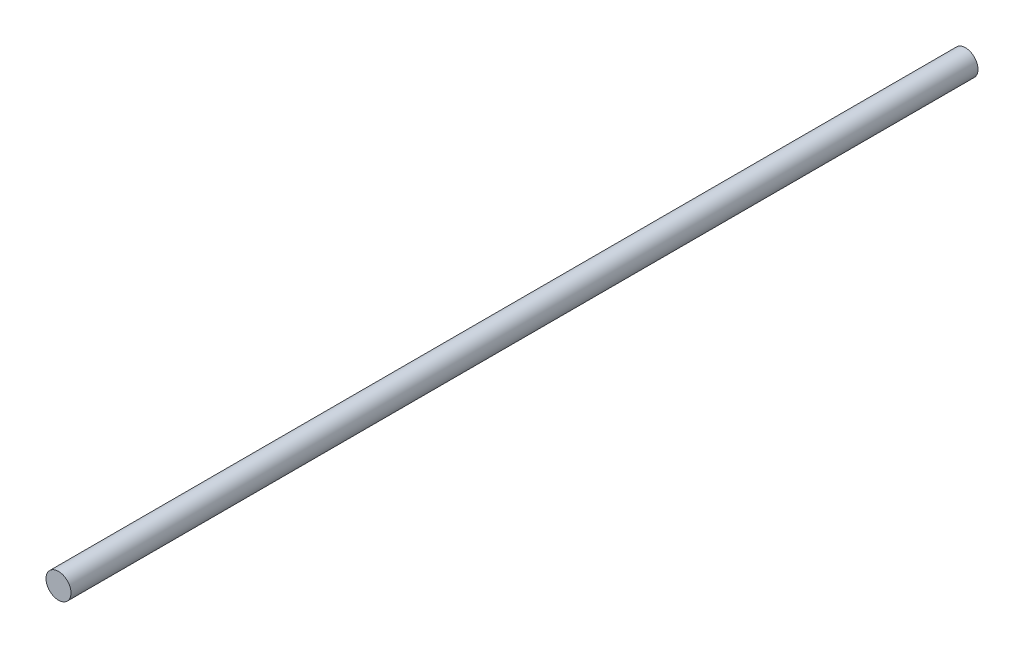
SolidWorks part; units mm, degrees
material "201 Annealed Stainless Steel (SS)"
ref_plane "Front Plane" through (0, 0, 0) normal (0, 0, 1) x (1, 0, 0)
ref_plane "Top Plane" through (0, 0, 0) normal (0, 1, 0) x (1, 0, 0)
ref_plane "Right Plane" through (0, 0, 0) normal (1, 0, 0) x (0, 0, -1)
sketch "Sketch1" plane through (0, 0, 0) normal (0, 0, 1) x (1, 0, 0)
  circle A0 centre (-32.4004, 2.1188) radius 4
extrude "Boss-Extrude1" add sketch "Sketch1" along normal blind 290
